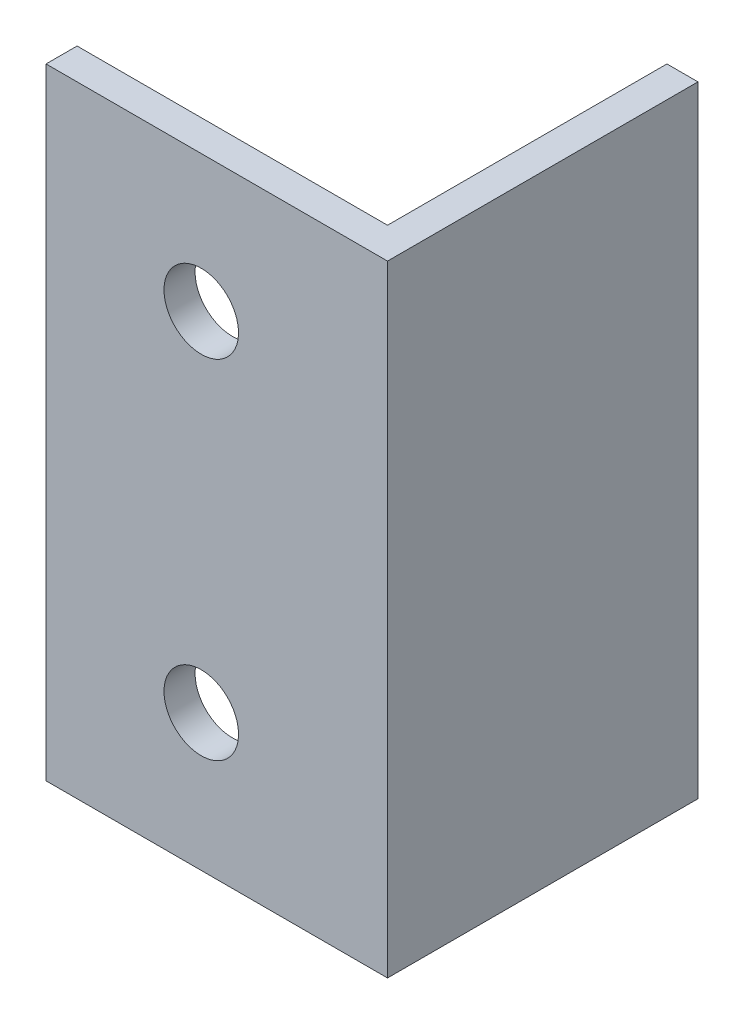
SolidWorks part; units mm, degrees
ref_plane "Front Plane" through (0, 0, 0) normal (0, 0, 1) x (1, 0, 0)
ref_plane "Top Plane" through (0, 0, 0) normal (0, 1, 0) x (1, 0, 0)
ref_plane "Right Plane" through (0, 0, 0) normal (1, 0, 0) x (0, 0, -1)
sketch "Sketch1" plane through (0, 0, 0) normal (0, 1, 0) x (1, 0, 0)
  line L0 (0, 0) -> (50, 0)
  line L5 (50, 0) -> (50, 45)
  line L6 (50, 45) -> (55, 45)
  line L7 (55, 45) -> (55, -5)
  line L8 (55, -5) -> (0, -5)
  line L9 (0, -5) -> (0, 0)
  dimension "D1" = 50
  dimension "D2" = 5
  dimension "D3" = 5
  dimension "D4" = 50
extrude "Boss-Extrude2" add sketch "Sketch1" along normal blind 100
sketch "Sketch2" plane through (0, 0, 0) normal (0, 0, -1) x (-1, 0, 0)
  line L0 (-50, 50) -> (0, 50) construction
  line L1 (-50, 100) -> (-50, 0) construction
  line L2 (0, 100) -> (0, 0) construction
  line L3 (-25, 0) -> (-25, 100)
  line L4 (-50, 100) -> (0, 100) construction
  circle A0 centre (-25, 78) radius 6
  circle A1 centre (-25, 22) radius 6
  point P11 (-25, 50)
  dimension "D1" = 12
  dimension "D2" = 28
  dimension "D3" = 28
extrude "Cut-Extrude1" cut sketch "Sketch2" against normal blind 100 contours L3 A1 | L3 A1 | L3 A0 | L3 A0
